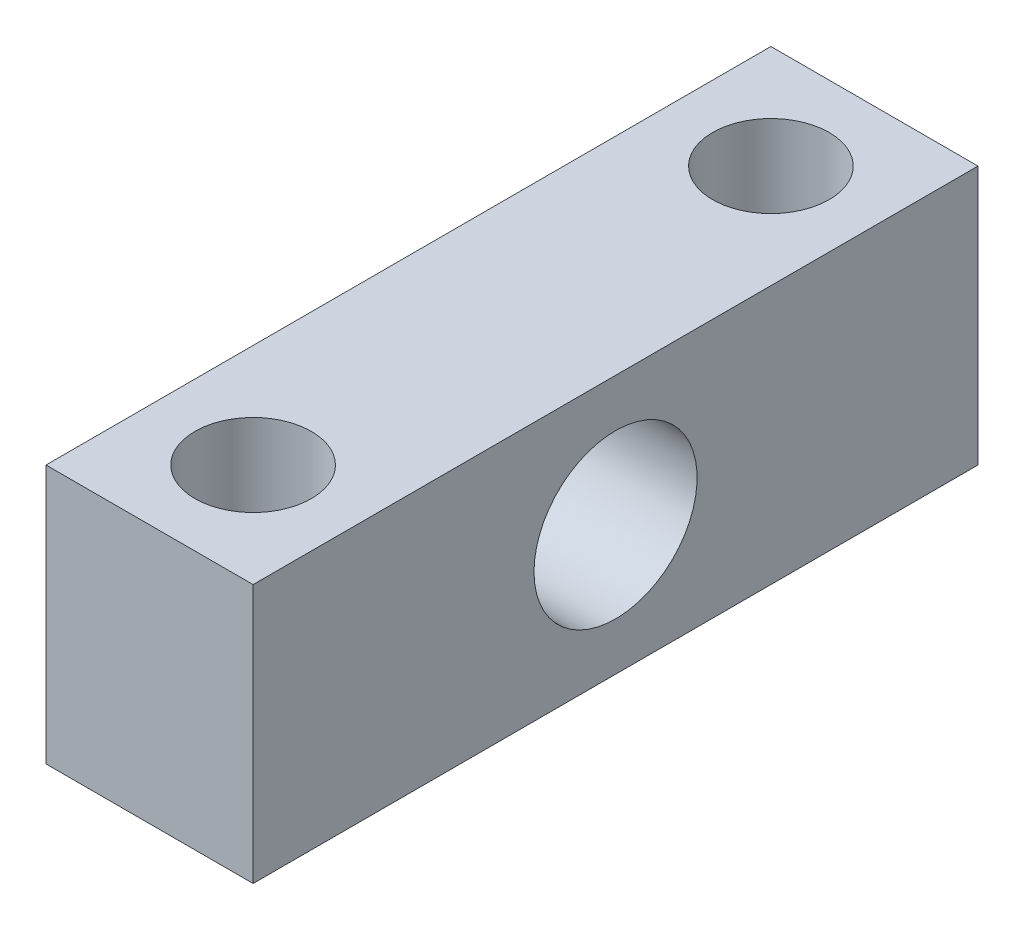
SolidWorks part; units mm, degrees
ref_plane "Front" through (0, 0, 0) normal (0, 0, 1) x (1, 0, 0)
ref_plane "Top" through (0, 0, 0) normal (0, 1, 0) x (1, 0, 0)
ref_plane "Right" through (0, 0, 0) normal (1, 0, 0) x (0, 0, -1)
sketch "Esquisse1" plane through (0, 0, 0) normal (0, 0, 1) x (1, 0, 0)
  line L1 (0, 0) -> (8, 0)
  line L2 (0, 0) -> (0, 10)
  line L3 (0, 10) -> (8, 10)
  line L4 (8, 0) -> (8, 10)
  dimension "D1" = 8
  dimension "D2" = 10
extrude "Boss.-Extru.1" add sketch "Esquisse1" along normal blind 28
sketch "Esquisse2" plane through (0, 10, 0) normal (0, 1, 0) x (1, 0, 0)
  line L0 (4, 0) -> (4, -28) construction
  line L1 (8, 0) -> (0, 0) construction
  line L2 (8, -28) -> (0, -28) construction
  line L3 (4, -14) -> (0, -14) construction
  line L4 (0, -28) -> (0, 0) construction
  circle A0 centre (4, -24) radius 2.25
  circle A1 centre (4, -4) radius 2.25
  dimension "D1" = 20
  dimension "D2" = 4.5
extrude "Enlèv. mat.-Extru.1" cut sketch "Esquisse2" against normal through all
sketch "Esquisse3" plane through (0, 0, 0) normal (-1, 0, 0) x (0, 0, 1)
  line L0 (14, 0) -> (14, 10) construction
  line L1 (28, 0) -> (0, 0) construction
  line L2 (28, 10) -> (0, 10) construction
  circle A0 centre (14, 5) radius 3.15
  dimension "D1" = 6.3
extrude "Enlèv. mat.-Extru.2" cut sketch "Esquisse3" against normal through all both and the other way through all
sketch "Esquisse4" plane through (0, 0, 0) normal (-1, 0, 0) x (0, 0, 1)
  circle A0 centre (14, 5) radius 3.65
  dimension "D1" = 7.3
extrude "Enlèv. mat.-Extru.3" cut sketch "Esquisse4" against normal blind 1
